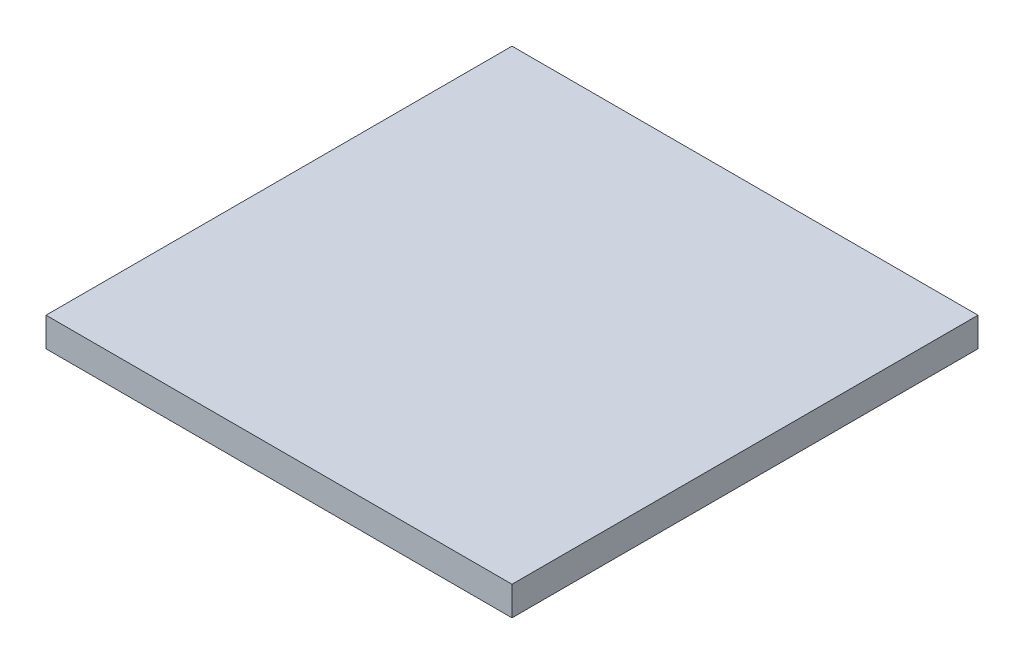
SolidWorks part; units mm, degrees
ref_plane "Front Plane" through (0, 0, 0) normal (0, 0, 1) x (1, 0, 0)
ref_plane "Top Plane" through (0, 0, 0) normal (0, 1, 0) x (1, 0, 0)
ref_plane "Right Plane" through (0, 0, 0) normal (1, 0, 0) x (0, 0, -1)
sketch "Sketch1" plane through (0, 0, 0) normal (0, 1, 0) x (1, 0, 0)
  line L1 (0, 0) -> (76.2, 0)
  line L2 (0, 0) -> (0, -76.2)
  line L3 (0, -76.2) -> (76.2, -76.2)
  line L4 (76.2, 0) -> (76.2, -76.2)
  dimension "D1" = 76.2
  dimension "D2" = 76.2
extrude "Boss-Extrude1" add sketch "Sketch1" along normal blind 4.7625 contours L1 L4 L3 L2
